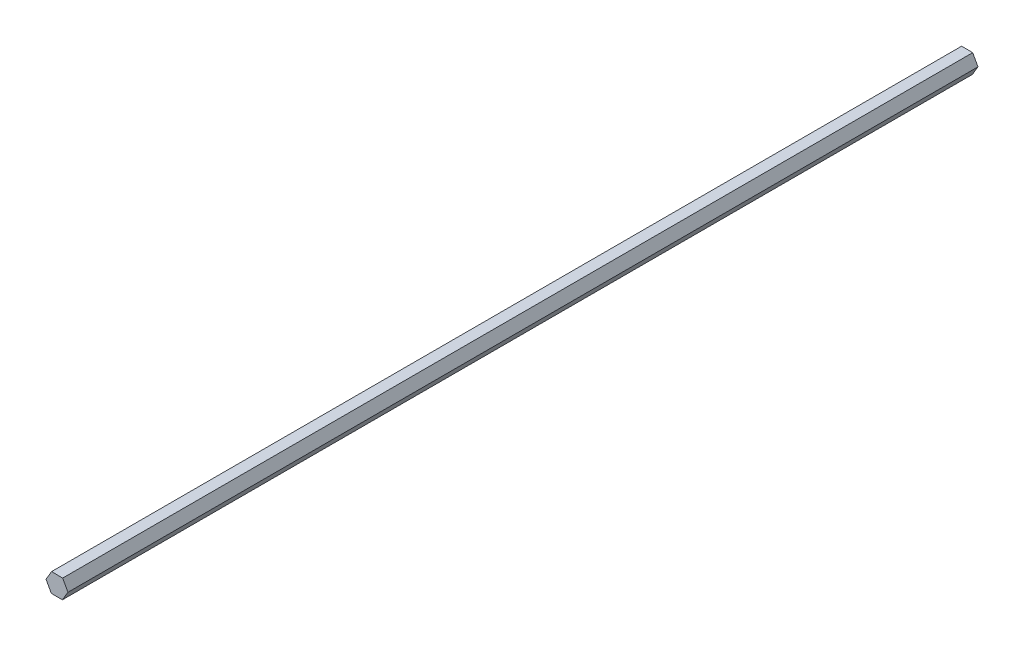
SolidWorks part; units mm, degrees
ref_plane "Front Plane" through (0, 0, 0) normal (0, 0, 1) x (1, 0, 0)
ref_plane "Top Plane" through (0, 0, 0) normal (0, 1, 0) x (1, 0, 0)
ref_plane "Right Plane" through (0, 0, 0) normal (1, 0, 0) x (0, 0, -1)
sketch "Sketch2" plane through (0, 0, 0) normal (0, 0, 1) x (1, 0, 0)
  line L1 (-0.0725, -2.4962) -> (3.3965, 3.2898)
  line L2 (3.3965, 3.2898) -> (0.1203, 9.187)
  line L3 (0.1203, 9.187) -> (-6.6251, 9.2984)
  line L4 (-6.6251, 9.2984) -> (-10.0941, 3.5124)
  line L5 (-10.0941, 3.5124) -> (-6.8179, -2.3849)
  line L6 (-6.8179, -2.3849) -> (-0.0725, -2.4962)
  circle A0 centre (-3.3488, 3.4011) radius 5.8424 construction
  dimension "D1" = 6.7462
extrude "Boss-Extrude1" add sketch "Sketch2" along normal blind 558.8
